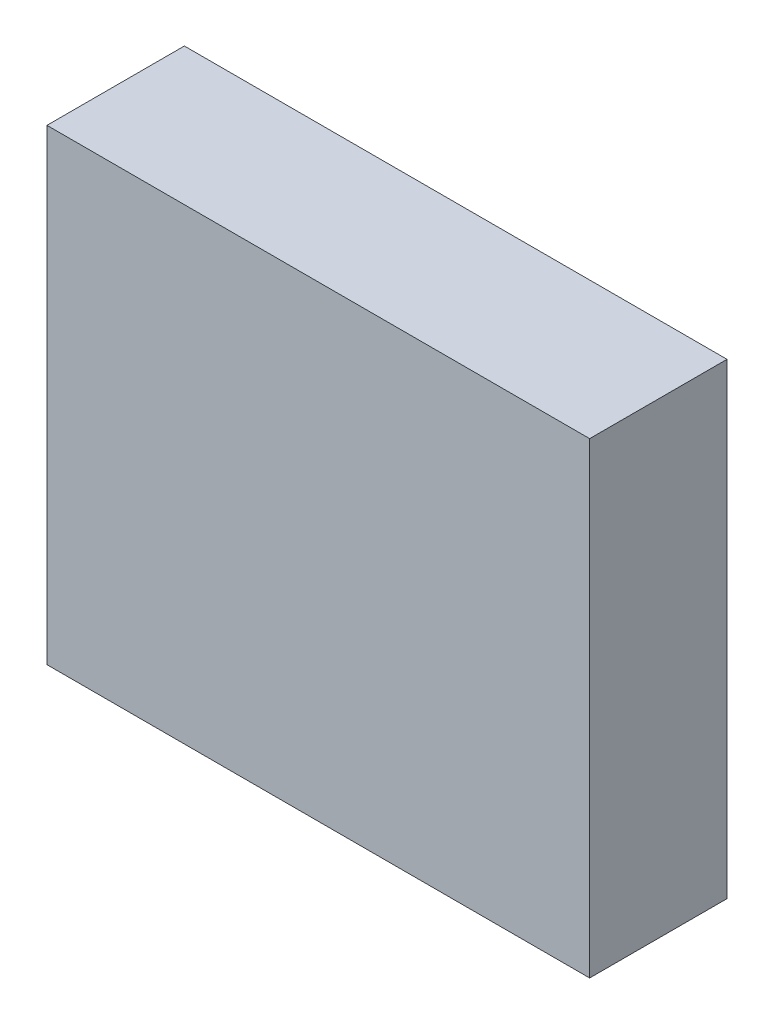
SolidWorks part; units mm, degrees
ref_plane "Front Plane" through (0, 0, 0) normal (0, 0, 1) x (1, 0, 0)
ref_plane "Top Plane" through (0, 0, 0) normal (0, 1, 0) x (1, 0, 0)
ref_plane "Right Plane" through (0, 0, 0) normal (1, 0, 0) x (0, 0, -1)
sketch "Sketch1" plane through (0, 0, 0) normal (0, 0, 1) x (1, 0, 0)
  line L1 (-39.5, -34) -> (39.5, -34)
  line L2 (-39.5, -34) -> (-39.5, 34)
  line L3 (-39.5, 34) -> (39.5, 34)
  line L4 (39.5, -34) -> (39.5, 34)
  line L5 (0, 34) -> (0, -34) construction
  line L6 (-39.5, 0) -> (39.5, 0) construction
  point P0 (0, 0)
  dimension "D1" = 79
  dimension "D2" = 68
extrude "Mold Base" add sketch "Sketch1" along normal blind 20
sketch "Sketch2" plane through (0, 0, 0) normal (0, 0, -1) x (-1, 0, 0)
  line L0 (-39.5, 34) -> (39.5, 34) construction
  line L1 (-34.5, -29) -> (34.5, -29)
  line L2 (-34.5, -29) -> (-34.5, 29)
  line L3 (-34.5, 29) -> (34.5, 29)
  line L4 (34.5, -29) -> (34.5, 29)
  line L5 (0, 29) -> (0, -29) construction
  line L6 (-34.5, 0) -> (34.5, 0) construction
  line L7 (-39.5, -34) -> (-39.5, 34) construction
  point P0 (0, 0)
  dimension "D1" = 5
  dimension "D2" = 5
extrude "Mold Cut" cut sketch "Sketch2" against normal blind 10
sketch "Sketch3" plane through (0, 0, 10) normal (0, 0, -1) x (-1, 0, 0)
  line L0 (0, 2.5) -> (0, -2.5) construction
  line L1 (0, 2.5) -> (0, -2.5)
  arc A0 (0, -2.5) -> (0, 2.5) centre (0, 0) ccw
  dimension "D1" = 5
revolve "Mold" cut sketch "Sketch3" angle 360 about L0
pattern_linear "LPattern1" count 3 spacing 10 along (0, 1, 0) count 3 spacing 10 along (-1, 0, 0) of "Mold"
pattern_linear "LPattern2" count 3 spacing 10 along (1, 0, 0) count 3 spacing 10 along (0, -1, 0) of "LPattern1", "Mold"
